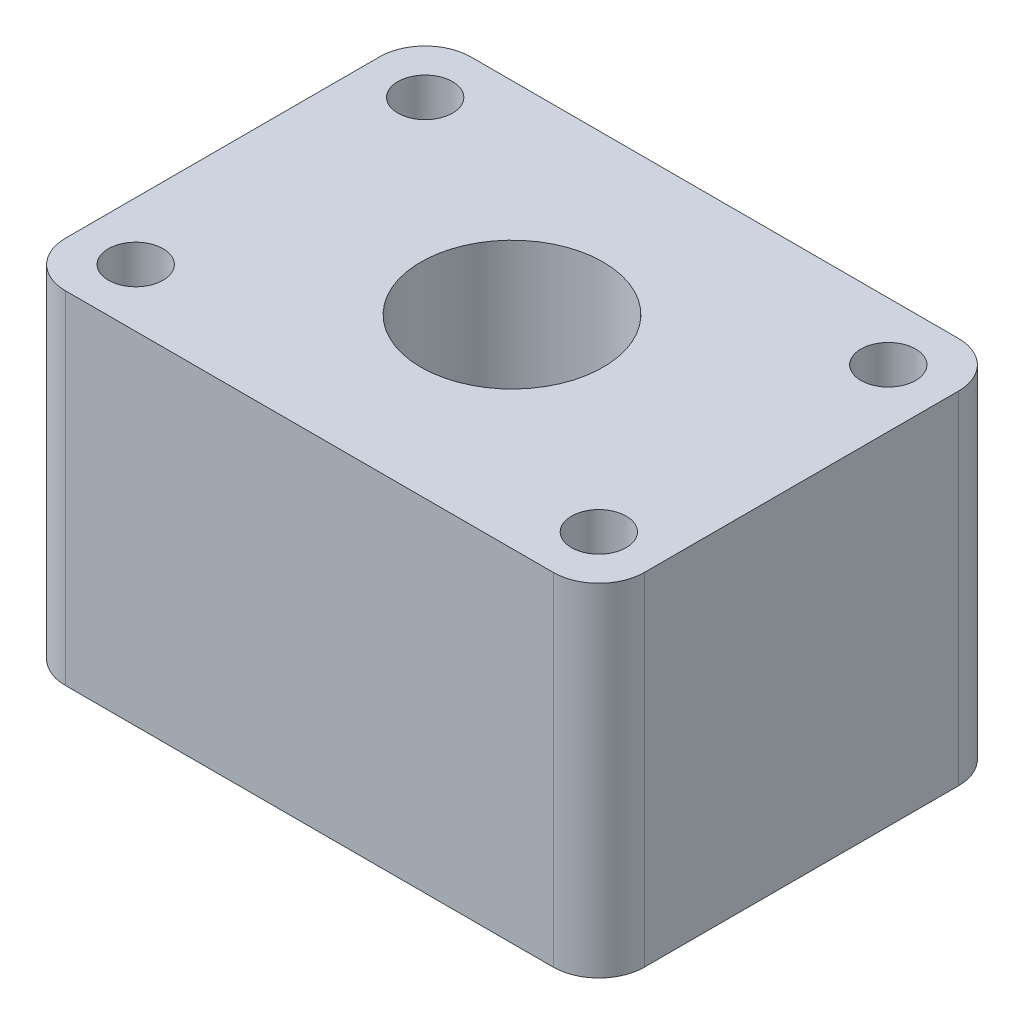
SolidWorks part; units mm, degrees
ref_plane "Front Plane" through (0, 0, 0) normal (0, 0, 1) x (1, 0, 0)
ref_plane "Top Plane" through (0, 0, 0) normal (0, 1, 0) x (1, 0, 0)
ref_plane "Right Plane" through (0, 0, 0) normal (1, 0, 0) x (0, 0, -1)
sketch "Sketch1" plane through (0, 0, 0) normal (0, 1, 0) x (1, 0, 0)
  line L1 (-12.7, 8.89) -> (12.7, 8.89)
  line L2 (-12.7, 8.89) -> (-12.7, -8.89)
  line L3 (-12.7, -8.89) -> (12.7, -8.89)
  line L4 (12.7, 8.89) -> (12.7, -8.89)
  line L5 (-12.7, 8.89) -> (12.7, -8.89) construction
  line L6 (-12.7, -8.89) -> (12.7, 8.89) construction
  point P0 (0, 0)
  dimension "D1" = 25.4
  dimension "D2" = 17.78
extrude "Boss-Extrude1" add sketch "Sketch1" along normal blind 15 contours L1 L4 L3 L2
sketch "Sketch2" plane through (0, 0, 0) normal (0, -1, 0) x (1, 0, 0)
  line L1 (-7, 4.5) -> (7, 4.5)
  line L2 (-7, 4.5) -> (-7, -4.5)
  line L3 (-7, -4.5) -> (7, -4.5)
  line L4 (7, 4.5) -> (7, -4.5)
  line L5 (-7, 4.5) -> (7, -4.5) construction
  line L6 (-7, -4.5) -> (7, 4.5) construction
  point P0 (0, 0)
  dimension "D1" = 14
  dimension "D2" = 9
extrude "Cut-Extrude1" cut sketch "Sketch2" against normal blind 4
sketch "Sketch3" plane through (0, 15, 0) normal (0, 1, 0) x (1, 0, 0)
  circle A0 centre (0, 0) radius 4
  dimension "D1" = 8
extrude "Cut-Extrude2" cut sketch "Sketch3" against normal blind 25
sketch "Sketch4" plane through (0, 0, 0) normal (0, -1, 0) x (1, 0, 0)
  line L1 (-10.16, -6.35) -> (10.16, -6.35) construction
  line L2 (-10.16, -6.35) -> (-10.16, 6.35) construction
  line L3 (-10.16, 6.35) -> (10.16, 6.35) construction
  line L4 (10.16, -6.35) -> (10.16, 6.35) construction
  line L5 (-10.16, -6.35) -> (10.16, 6.35) construction
  line L6 (-10.16, 6.35) -> (10.16, -6.35) construction
  circle A0 centre (-10.16, -6.35) radius 1.2
  circle A1 centre (-10.16, 6.35) radius 1.2
  circle A2 centre (10.16, 6.35) radius 1.2
  circle A3 centre (10.16, -6.35) radius 1.2
  point P0 (0, 0)
  dimension "D3" = 2.4
  dimension "D4" = 2.4
  dimension "D5" = 2.4
  dimension "D6" = 2.4
  dimension "D1" = 12.7
  dimension "D2" = 20.32
extrude "Cut-Extrude3" cut sketch "Sketch4" against normal blind 25
fillet "Fillet1" radius 2 4 edges at (-12.7, 7.5, 8.89) (12.7, 7.5, 8.89) (12.7, 7.5, -8.89) (-12.7, 7.5, -8.89)
chamfer "Chamfer1" distance 0.5 angle 45 8 edges at (7, 0, 0) (0, 0, 4.5) (-7, 0, 0) (0, 0, -4.5) (-10.16, 0, -7.55) (10.16, 0, -7.55) (10.16, 0, 5.15) (-10.16, 0, 5.15)
sketch "Sketch5" plane through (0, 0, 0) normal (0, -1, 0) x (1, 0, 0)
  line L0 (-10.7, -8.89) -> (10.7, -8.89) construction
  line L1 (8, -7.39) -> (-8, -7.39)
  line L2 (8, -7.39) -> (8, -5.39)
  line L3 (8, -5.39) -> (-8, -5.39)
  line L4 (-8, -7.39) -> (-8, -5.39)
  line L5 (8, -7.39) -> (-8, -5.39) construction
  line L6 (8, -5.39) -> (-8, -7.39) construction
  point P0 (0, -6.39)
  point P7 (0, -8.89)
  dimension "D1" = 2.5
  dimension "D2" = 2
  dimension "D3" = 16
extrude "Cut-Extrude4" cut sketch "Sketch5" against normal blind 3 and the other way blind 7
